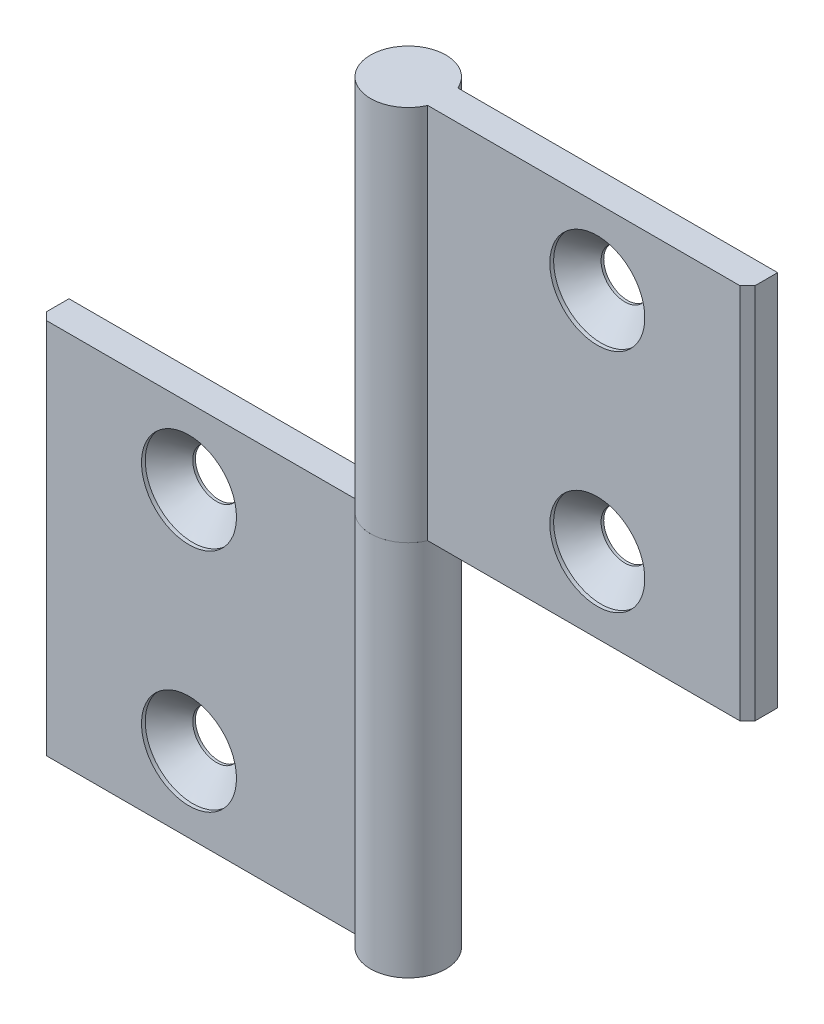
SolidWorks part; units mm, degrees
material "Алюминиевый сплав"
ref_plane "Спереди" through (0, 0, 0) normal (0, 0, 1) x (1, 0, 0)
ref_plane "Сверху" through (0, 0, 0) normal (0, 1, 0) x (1, 0, 0)
ref_plane "Справа" through (0, 0, 0) normal (1, 0, 0) x (0, 0, -1)
sketch "Эскиз1" plane through (0, 0, 0) normal (0, 1, 0) x (1, 0, 0)
  line L0 (-4.5826, 2) -> (-47, 2)
  line L1 (-47, 2) -> (-47, -1)
  line L2 (-47, -1) -> (-46, -2)
  line L3 (-46, -2) -> (-4.5826, -2)
  line L5 (-25.7913, 2) -> (-25.7913, -2) construction
  arc A0 (-4.5826, -2) -> (-4.5826, 2) centre (0, 0) ccw
  point P1 (-25.7913, 0)
  dimension "D5" = 5
  dimension "D1" = 42
  dimension "D2" = 4
  dimension "D3" = 3
  dimension "D4" = 45
extrude "Бобышка-Вытянуть1" add sketch "Эскиз1" along normal mid plane 50
hole_wizard "Зенковка для винта с полупотайной головкой M61" positions "Эскиз4" profile "Эскиз6" countersink size "M6" standard "ISO" end condition through all
sketch "Эскиз4" plane through (0, 0, 2) normal (0, 0, 1) x (1, 0, 0)
  line L0 (-27.0826, 15) -> (-27.0826, -15)
  line L2 (0.2087, -18.4577) -> (0.2087, 25) construction
  line L4 (5, 25) -> (-4.5826, 25) construction
  line L5 (-4.5826, 25) -> (-4.5826, -25) construction
  point P0 (-27.0826, 15)
  point P2 (-27.0826, -15)
  point P9 (-27.0826, 0)
  dimension "D1" = 30
  dimension "D2" = 22.5
sketch "Эскиз6" plane through (-27.0826, 15, 2) normal (1, 0, 0) x (0, -1, 0)
  line L0 (0, 0) -> (0, 7)
  line L1 (0, 7) -> (3.15, 7)
  line L2 (3.15, 7) -> (3.15, 3.65)
  line L3 (3.15, 3.65) -> (6.3, 0.5)
  line L4 (6.3, 0.5) -> (6.3, 0)
  line L6 (6.3, 0) -> (0, 0)
  line L7 (-3.15, 3.65) -> (-6.3, 0.5) construction
  line L11 (0, -6.35) -> (0, 107.95) construction
  dimension "Диаметр сквозного отверстия" = 6.3
  dimension "Глубина сквозного отверстия" = 7
  dimension "Диаметр зенковки" = 12.6
  dimension "Угол зенковки" = 90
  dimension "Утопленность" = 0.5
sketch "Угол раскрытия" plane through (0, 25, 0) normal (0, 1, 0) x (1, 0, 0)
  line L0 (0, 0) -> (0, -10)
  line L7 (-4.5826, 2) -> (-47, 2) construction
  dimension "D1" = 10
  dimension "D2" = 90
pattern_circular "Круговой массив1" count 2 over 360 about axis through (0, 25, 0) along (0, 0, 1) of bodies 106
